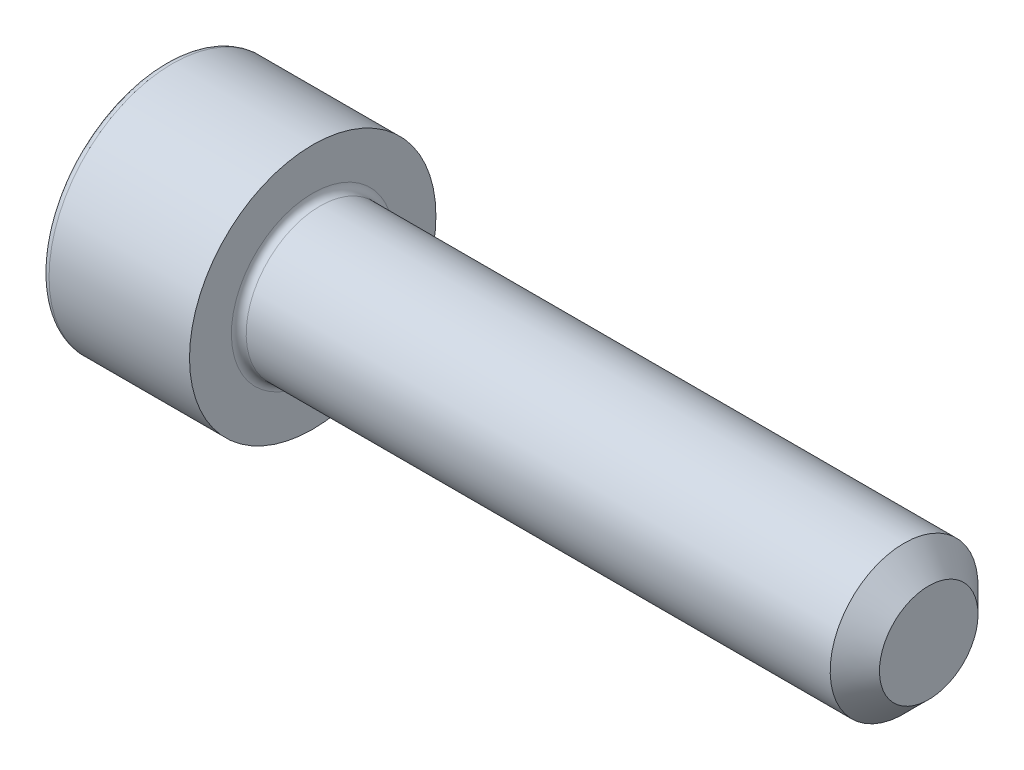
SolidWorks part; units mm, degrees
ref_plane "Спереди" through (0, 0, 0) normal (0, 0, 1) x (1, 0, 0)
ref_plane "Сверху" through (0, 0, 0) normal (0, 1, 0) x (1, 0, 0)
ref_plane "Справа" through (0, 0, 0) normal (1, 0, 0) x (0, 0, -1)
sketch "Эскиз1" plane through (0, 0, 0) normal (0, 0, 1) x (1, 0, 0)
  line L0 (0, 0) -> (0, 5)
  line L1 (0, 5) -> (6, 5)
  line L2 (6, 5) -> (6, 3)
  line L3 (6, 3) -> (31, 3)
  line L4 (31, 3) -> (31, 0)
  line L5 (31, 0) -> (0, 0) construction
  line L6 (0, 0) -> (31, 0)
  dimension "D1" = 10
  dimension "D2" = 6
  dimension "D3" = 6
  dimension "D4" = 25
revolve "Повернуть1" add sketch "Эскиз1" angle 360 about L5
cosmetic thread "Условное изображение резьбы1" parameters "D2"=4.891
sketch "Эскиз2" plane through (0, 0, 0) normal (-1, 0, 0) x (0, 0, 1)
  line L1 (-1.4434, 2.5) -> (-2.8868, 0)
  line L2 (-2.8868, 0) -> (-1.4434, -2.5)
  line L3 (-1.4434, -2.5) -> (1.4434, -2.5)
  line L4 (1.4434, -2.5) -> (2.8868, 0)
  line L5 (2.8868, 0) -> (1.4434, 2.5)
  line L6 (1.4434, 2.5) -> (-1.4434, 2.5)
  circle A0 centre (0, 0) radius 2.5 construction
  dimension "D1" = 5
extrude "Вырез-Вытянуть1" cut sketch "Эскиз2" against normal blind 2.5
fillet "Скругление1" radius 0.3 2 edges at (0, 5, 0) (6, 3, 0)
chamfer "Фаска1" distance 1 angle 45 1 edges at (31, 3, 0)
